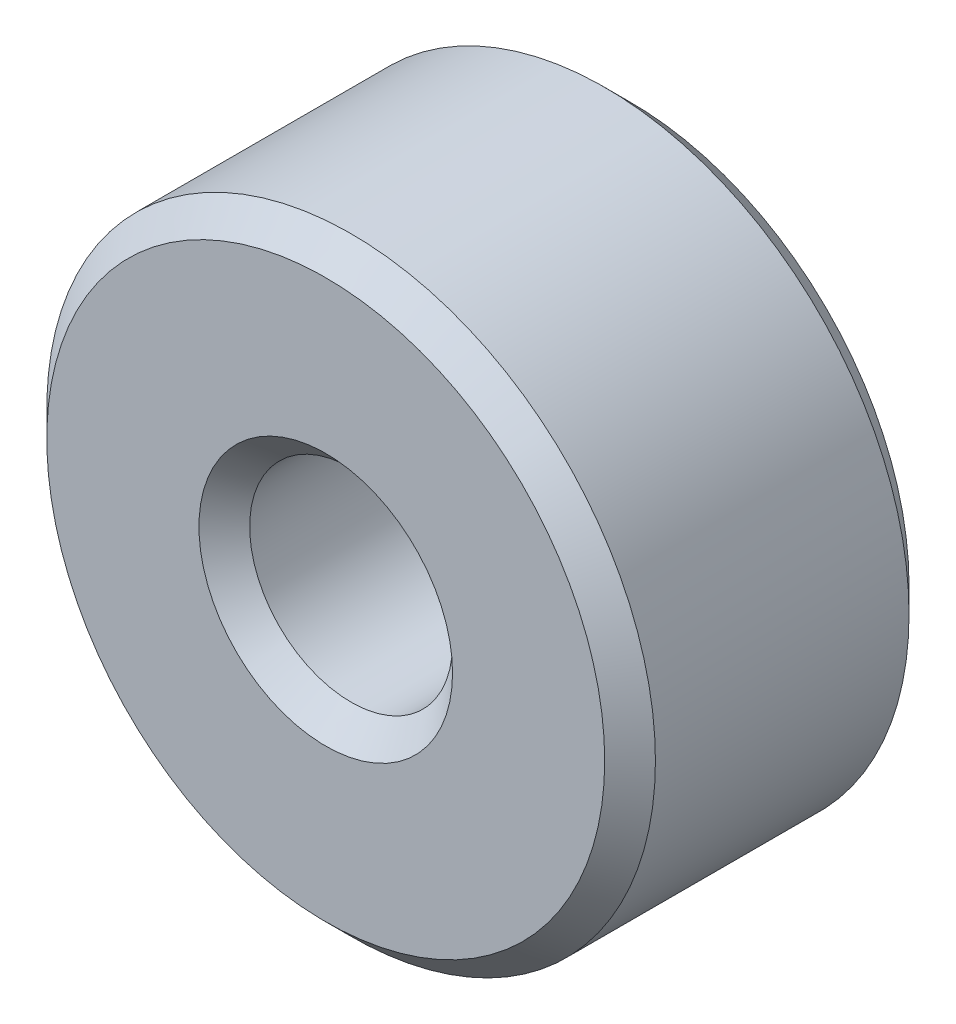
SolidWorks part; units mm, degrees
ref_plane "Front Plane" through (0, 0, 0) normal (0, 0, 1) x (1, 0, 0)
ref_plane "Top Plane" through (0, 0, 0) normal (0, 1, 0) x (1, 0, 0)
ref_plane "Right Plane" through (0, 0, 0) normal (1, 0, 0) x (0, 0, -1)
sketch "Sketch1" plane through (0, 0, 0) normal (0, 0, 1) x (1, 0, 0)
  circle A0 centre (0, 0) radius 1
  dimension "D1" = 2
extrude "Extrude-Thin1" add sketch "Sketch1" along normal blind 3 thin
chamfer "Chamfer1" distance 0.25 angle 45 4 edges at (1, 0, 0) (3, 0, 0) (1, 0, 3) (3, 0, 3)
scale "Scale1" scale about centroid uniform scaling yes scale factor 10
